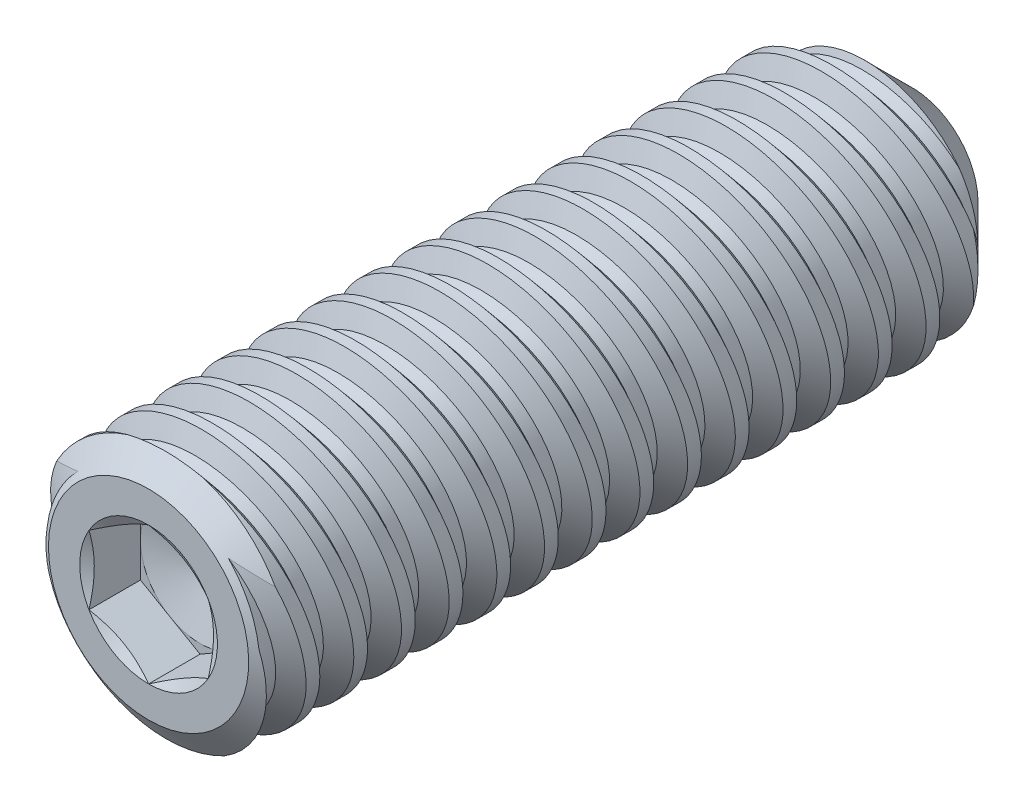
SolidWorks part; units mm, degrees
ref_plane "Front" through (0, 0, 0) normal (0, 0, 1) x (1, 0, 0)
ref_plane "Top" through (0, 0, 0) normal (0, 1, 0) x (1, 0, 0)
ref_plane "Right" through (0, 0, 0) normal (1, 0, 0) x (0, 0, -1)
sketch "Sketch22" plane through (0, 0, 0) normal (1, 0, 0) x (0, 0, -1)
  line L0 (-6.35, 0) -> (-6.35, 1.6662)
  line L1 (-6.35, 1.6662) -> (-6.0583, 2.0828)
  line L2 (-6.0583, 2.0828) -> (5.3721, 2.0828)
  line L3 (5.3721, 2.0828) -> (6.35, 1.1049)
  line L4 (6.35, 1.1049) -> (5.6861, 0) construction
  line L5 (6.35, 0) -> (-6.35, 0)
  line L6 (5.6861, 0) -> (6.35, 0) construction
  line L7 (6.35, 0) -> (6.35, 1.1049)
  line L8 (6.35, -1.1049) -> (5.6861, 0) construction
  line L9 (-6.0583, -2.0828) -> (5.3721, -2.0828) construction
  line L10 (6.35, -1.1049) -> (-6.35, -1.1049) construction
  line L11 (-6.35, -1.1049) -> (-6.35, 0) construction
  line L12 (0, -1.1049) -> (0, 0) construction
  dimension "Screw Dia" = 4.1656
  dimension "Length" = 12.7
  dimension "D3" = 35
  dimension "Cup Point Dia" = 2.2098
  dimension "D5" = 118
  dimension "D6" = 45
  dimension "D7" = 3.3325
revolve "Revolve1" add sketch "Sketch22" angle 360 about L6
sketch "Sketch6" plane through (0, 0, 0) normal (1, 0, 0) x (0, 0, -1)
  line L0 (4.1238, 2.0828) -> (4.9176, -2.0828) construction
  line L1 (-6.0583, 2.0828) -> (5.3721, 2.0828) construction
  line L2 (-6.0583, -2.0828) -> (5.3721, -2.0828) construction
  line L3 (4.1238, 2.0828) -> (4.2213, 2.1014) construction
  line L4 (4.7403, 1.7629) -> (4.5454, 1.7258)
  line L5 (4.5454, 1.7258) -> (4.2213, 2.1014)
  line L6 (4.7403, 1.7629) -> (4.9036, 2.2314)
  line L7 (4.9036, 2.2314) -> (4.2213, 2.1014)
  line L8 (4.5784, 2.0828) -> (5.3721, -2.0828) construction
  line L9 (5.8266, 0.1622) -> (4.1238, -0.1622) construction
  line L10 (4.5624, 2.1664) -> (4.6428, 1.7443) construction
  line L13 (4.1238, -2.0828) -> (4.1238, 2.0828) construction
  line L14 (4.1238, -2.0828) -> (4.9176, -2.0828) construction
  line L15 (4.9176, -2.0828) -> (5.3721, -2.0828) construction
  line L18 (4.1238, 2.0828) -> (4.5784, 2.0828) construction
  point P18 (4.9752, 0)
  dimension "D1" = 0.7937
  dimension "D2" = 0.1984
  dimension "D3" = 60
  dimension "D4" = 0.0992
  dimension "Pitch" = 0.7937
revolve "Cut-Revolve8" cut sketch "Sketch6" angle 360 about L9
pattern_linear "LPattern1" count 15 spacing 0.7937 along (0, 0, 1) count 2 spacing 0.7937 along (0, 0, -1) of "Cut-Revolve8"
sketch "Sketch23" plane through (0, 0, 6.35) normal (0, 0, 1) x (1, 0, 0)
  line L1 (0, 1.1457) -> (-0.9922, 0.5728)
  line L2 (-0.9922, 0.5728) -> (-0.9922, -0.5728)
  line L3 (-0.9922, -0.5728) -> (0, -1.1457)
  line L4 (0, -1.1457) -> (0.9922, -0.5728)
  line L5 (0.9922, -0.5728) -> (0.9922, 0.5728)
  line L6 (0.9922, 0.5728) -> (0, 1.1457)
  circle A0 centre (0, 0) radius 0.9922 construction
  dimension "Hex" = 1.9844
extrude "Cut-Extrude10" cut sketch "Sketch23" against normal blind 0.8573
sketch "Sketch24" plane through (0, 0, 6.35) normal (0, 0, 1) x (1, 0, 0)
  circle A0 centre (0, 0) radius 1.1457
extrude "Cut-Extrude11" cut sketch "Sketch24" against normal through all draft 60
sketch "Sketch26" plane through (0, 0, 5.4928) normal (0, 0, 1) x (1, 0, 0)
  circle A0 centre (0, 0) radius 0.9922 construction
  circle A1 centre (0, 0) radius 0.9922
extrude "Cut-Extrude12" cut sketch "Sketch26" against normal through all draft 75
equation "\"D2@Sketch6\"=\"Pitch@Sketch6\"/4"
equation "\"D4@Sketch6\"=\"Pitch@Sketch6\"/8"
equation "\"D1@Sketch6\"=\"Pitch@Sketch6\""
equation "\"D3@LPattern1\"=\"Pitch@Sketch6\""
equation "\"D1@LPattern1\"=(\"Length@Sketch22\"/\"Pitch@Sketch6\")-1"
equation "\"D4@LPattern1\"=\"Pitch@Sketch6\""
equation "\"D7@Sketch22\"=\"Screw Dia@Sketch22\"*.8"
